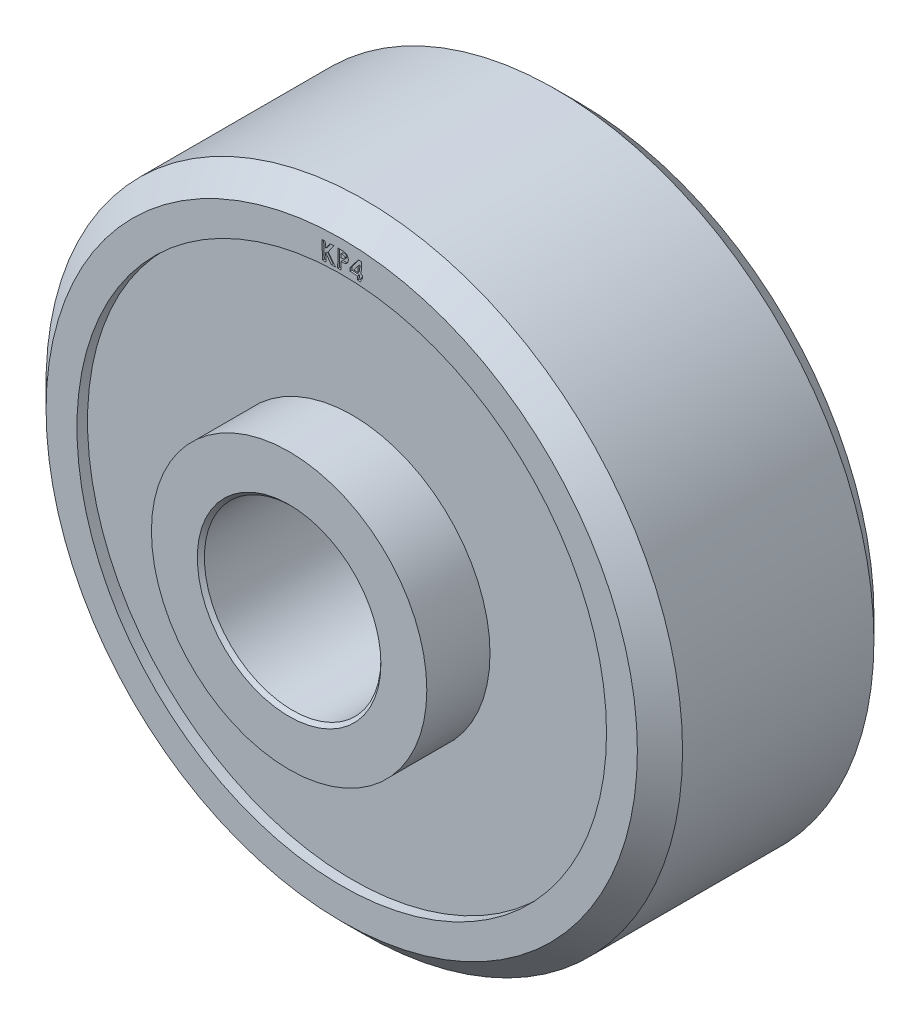
SolidWorks part; units mm, degrees
ref_plane "Front Plane" through (0, 0, 0) normal (0, 0, 1) x (1, 0, 0)
ref_plane "Top Plane" through (0, 0, 0) normal (0, 1, 0) x (1, 0, 0)
ref_plane "Right Plane" through (0, 0, 0) normal (1, 0, 0) x (0, 0, -1)
sketch "Sketch1" plane through (0, 0, 0) normal (1, 0, 0) x (0, 0, -1)
  line L0 (0, 0) -> (8.5758, 0) construction
  line L1 (-6.1468, 3.302) -> (-6.1468, 4.953)
  line L2 (-6.1468, 4.953) -> (-3.8735, 4.953)
  line L3 (-3.8735, 4.953) -> (-3.8735, 9.525)
  line L4 (-3.8735, 9.525) -> (-4.2545, 9.525)
  line L5 (-4.2545, 9.525) -> (-4.2545, 10.635)
  line L6 (-4.2545, 10.635) -> (-3.4417, 11.4478)
  line L7 (-3.4417, 11.4478) -> (3.4417, 11.4478)
  line L8 (-6.0198, 3.175) -> (6.0198, 3.175)
  line L9 (0, 0) -> (0, 12.798) construction
  line L10 (4.2545, 10.635) -> (3.4417, 11.4478)
  line L11 (4.2545, 9.525) -> (4.2545, 10.635)
  line L12 (3.8735, 9.525) -> (4.2545, 9.525)
  line L13 (3.8735, 4.953) -> (3.8735, 9.525)
  line L14 (6.1468, 4.953) -> (3.8735, 4.953)
  line L15 (6.1468, 3.302) -> (6.1468, 4.953)
  line L16 (6.0198, 3.175) -> (6.1468, 3.302)
  line L17 (-6.1468, 3.302) -> (-6.0198, 3.175)
  point P3 (-6.1468, 3.175)
  point P19 (6.1468, 3.175)
  dimension "D1" = 6.35
  dimension "D2" = 9.906
  dimension "D3" = 12.2936
  dimension "D4" = 8.509
  dimension "D5" = 0.381
  dimension "D6" = 19.05
  dimension "D7" = 45
  dimension "D8" = 0.8128
  dimension "D9" = 22.8956
revolve "Revolve1" add sketch "Sketch1" angle 360 about L0
sketch "Sketch2" plane through (0, 0, 4.2545) normal (0, 0, 1) x (1, 0, 0)
  line L0 (0, 0) -> (0, 9.652) construction
  arc A1 (-0.7612, 9.6219) -> (0.7612, 9.6219) centre (0, 0) cw construction
  text T0 "KP4" font "Century Gothic" height 0.635
  dimension "D1" = 9.652
  dimension "D2" = 1.524
extrude "Cut-Extrude1" cut sketch "Sketch2" against normal blind 0.0635
